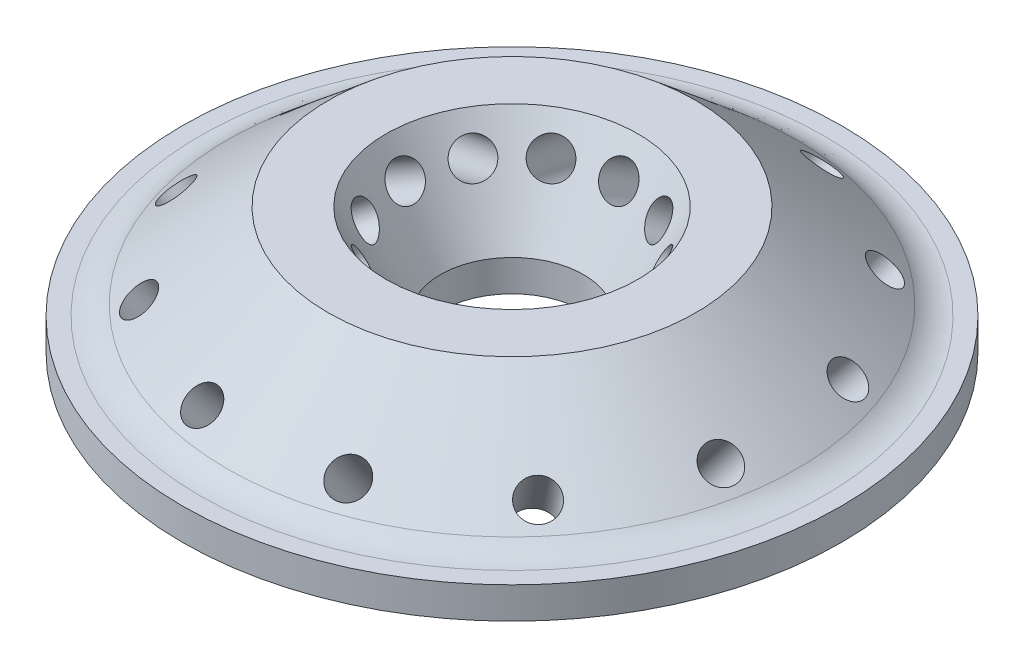
SolidWorks part; units mm, degrees
other "Markup1"
sketch "Sketch26" plane through (-39.8296, 20.32, 39.8296) normal (-0.1821, 0.7426, 0.6445) x (0.9804, 0.0872, 0.1766)
material "6061-T6 (SS)"
ref_plane "Front Plane" through (0, 0, 0) normal (0, 0, 1) x (1, 0, 0)
ref_plane "Top Plane" through (0, 0, 0) normal (0, 1, 0) x (1, 0, 0)
ref_plane "Right Plane" through (0, 0, 0) normal (1, 0, 0) x (0, 0, -1)
sketch "Sketch1" plane through (0, 0, 0) normal (0, 1, 0) x (1, 0, 0)
  circle A0 centre (0, 0) radius 69.85
  dimension "D1" = 139.7
extrude "Boss-Extrude1" add sketch "Sketch1" along normal blind 8.89
sketch "Sketch2" plane through (0, 8.89, 0) normal (0, 1, 0) x (1, 0, 0)
  circle A0 centre (0, 0) radius 15.24
  circle A1 centre (0, 0) radius 22.225
  dimension "D1" = 30.48
  dimension "D2" = 44.45
extrude "Boss-Extrude2" add sketch "Sketch2" along normal blind 11.43
sketch "Sketch7" plane through (0, 0, 0) normal (0, 0, 1) x (1, 0, 0)
  line L0 (0, 0) -> (0, 20.32) construction
  line L1 (0, 20.32) -> (-15.24, 20.32) construction
  line L2 (15.24, 20.32) -> (-15.24, 20.32) construction
  line L3 (-15.24, 20.32) -> (-15.24, 8.89)
  line L4 (-15.24, 8.89) -> (-8.6409, 8.89)
  line L5 (-15.24, 20.32) -> (-8.6409, 8.89)
  line L7 (-13.0175, 16.4705) -> (-46.2039, -2.6896) construction
  line L8 (15.24, 8.89) -> (-15.24, 8.89) construction
  point P11 (0, 0)
  dimension "D1" = 60
  dimension "D2" = 4.445
revolve "Revolve2" add sketch "Sketch7" angle 360 about L0
ref_plane "Plane2" through (0, 0, 0) normal (0.3256, 0, 0.9455) x (0, 1, 0)
sketch "Sketch9" plane through (0, 0, 0) normal (-0.3256, 0, -0.9455) x (-0.9455, 0, 0.3256)
  line L0 (0, 0) -> (0, 20.32) construction
  line L1 (0, 20.32) -> (-22.225, 20.32) construction
  line L2 (22.225, 20.32) -> (-22.225, 20.32) construction
  line L3 (-22.225, 20.32) -> (-22.225, 8.89)
  line L4 (22.225, 8.89) -> (-22.225, 8.89) construction
  line L5 (-22.225, 20.32) -> (-35.8467, 8.89)
  line L6 (-35.8467, 8.89) -> (-22.225, 8.89)
  line L7 (-31.9538, 12.1566) -> (-16.8851, -5.8015) construction
  dimension "D1" = 40
  dimension "D2" = 12.7
revolve "Revolve3" add sketch "Sketch9" angle 360 about L0
ref_plane "Plane1" through (-2.6312, -1.5191, 0) normal (-0.866, -0.5, 0) x (0.5, -0.866, 0)
sketch "Sketch13" plane through (0, 0, 0) normal (0, -1, 0) x (1, 0, 0)
  circle A0 centre (0, 0) radius 14.2875
  circle A1 centre (0, 0) radius 25.4
  circle A2 centre (0, 0) radius 33.02
  circle A3 centre (0, 0) radius 41.275
  circle A4 centre (0, 0) radius 7.62
  dimension "D1" = 28.575
  dimension "D2" = 50.8
  dimension "D3" = 66.04
  dimension "D4" = 82.55
  dimension "D5" = 15.24
extrude "Cut-Extrude10" cut sketch "Sketch13" against normal blind 5.08 contours A3 A2 | A1 A0 | A4
fillet "Fillet3" radius 2.54 5 edges at (0, 5.08, -7.62) (0, 5.08, -25.4) (0, 5.08, -14.2875) (0, 5.08, -33.02) (0, 5.08, -41.275)
sketch "Sketch10" plane through (-2.6312, -1.5191, 0) normal (-0.866, -0.5, 0) x (0.5, -0.866, 0)
  circle A0 centre (-20.7726, 0) radius 2.1828
  dimension "D1" = 4.3656
extrude "Cut-Extrude5" cut sketch "Sketch10" against normal blind 2.54 and the other way blind 30.48
ref_plane "Plane3" through (18.1431, 22.8679, -6.2472) normal (-0.6078, -0.766, 0.2093) x (0.7243, -0.6428, -0.2494)
sketch "Sketch11" plane through (18.1431, 22.8679, -6.2472) normal (-0.6078, -0.766, 0.2093) x (0.7243, -0.6428, -0.2494)
  circle A0 centre (16.6639, 0) radius 2.1828
  dimension "D1" = 4.3656
extrude "Cut-Extrude6" cut sketch "Sketch11" against normal blind 3.175 and the other way blind 19.05
pattern_circular "CirPattern1" count 12 over 360 about axis through (0, 8.89, 0) along (0, -1, 0) of "Cut-Extrude6", "Cut-Extrude5"
sketch "Sketch12" plane through (0, 8.89, 0) normal (0, 1, 0) x (1, 0, 0)
  circle A0 centre (0, 0) radius 60.96 construction
  circle A1 centre (60.96, 0) radius 2.54
  dimension "D1" = 121.92
  dimension "D2" = 5.08
extrude "Cut-Extrude7" cut sketch "Sketch12" against normal through all
pattern_circular "CirPattern2" count 12 over 360 about axis through (0, 0, 0) along (0, 1, 0) of "Cut-Extrude7"
sketch "Sketch15" plane through (0, 8.89, 0) normal (0, 1, 0) x (1, 0, 0)
  circle A0 centre (0, 0) radius 5.715 construction
  circle A1 centre (0, 5.715) radius 1.3891
  dimension "D1" = 2.7781
  dimension "D2" = 11.43
extrude "Cut-Extrude11" cut sketch "Sketch15" against normal through all
pattern_circular "CirPattern3" count 8 over 360 about axis through (0, 0, 0) along (0, 1, 0) of "Cut-Extrude11"
sketch "Sketch16" plane through (0, 0, 0) normal (0, -1, 0) x (1, 0, 0)
  circle A0 centre (0, 0) radius 27.5717
  circle A1 centre (0, 0) radius 30.2133
  dimension "D1" = 2.6416
  dimension "D2" = 60.4266
extrude "Cut-Extrude12" cut sketch "Sketch16" against normal blind 1.3208
sketch "Sketch17" plane through (0, 0, 0) normal (0, -1, 0) x (1, 0, 0)
  circle A0 centre (0, 0) radius 9.3091
  circle A1 centre (0, 0) radius 11.9507
  dimension "D1" = 2.6416
  dimension "D2" = 23.9014
extrude "Cut-Extrude13" cut sketch "Sketch17" against normal blind 1.3208
sketch "Sketch18" plane through (0, 8.89, 0) normal (0, 1, 0) x (1, 0, 0)
  circle A0 centre (0, 0) radius 49.7967
  circle A1 centre (0, 0) radius 52.4383
  dimension "D1" = 2.6416
  dimension "D2" = 104.8766
extrude "Cut-Extrude14" cut sketch "Sketch18" against normal blind 1.3208
sketch "Sketch19" plane through (0, 0, 0) normal (0, -1, 0) x (1, 0, 0)
  circle A0 centre (0, 0) radius 52.4383
  circle A1 centre (0, 0) radius 49.7967
  dimension "D1" = 104.8766
  dimension "D2" = 2.6416
extrude "Cut-Extrude15" cut sketch "Sketch19" against normal blind 1.3208
sketch "Sketch21" plane through (0, 8.89, 0) normal (0, 1, 0) x (1, 0, 0)
  circle A0 centre (0, 0) radius 1.3891
  circle A1 centre (4.0411, 4.0411) radius 1.3891 construction
extrude "Cut-Extrude17" cut sketch "Sketch21" against normal through all
fillet "Fillet2" radius 5.08 1 edges at (0, 8.89, -35.8467)
sketch "Sketch23" plane through (0, 7.5692, 0) normal (0, 1, 0) x (1, 0, 0)
  circle A0 centre (0, 0) radius 39.8296
  circle A1 centre (0, 0) radius 75.5943
extrude "Cut-Extrude18" cut sketch "Sketch23" against normal through all both and the other way through all
sketch "Sketch24" plane through (0, 0, 0) normal (0, -1, 0) x (1, 0, 0)
  circle A0 centre (0, 0) radius 58.815
extrude "Cut-Extrude19" cut sketch "Sketch24" against normal up to surface (5.08 mm away) up to face at (0, 5.08, -22.86)
sketch "Sketch25" plane through (0, 8.89, 0) normal (0, 1, 0) x (1, 0, 0)
  circle A0 centre (0, 0) radius 8.6409
  circle A1 centre (0, 0) radius 8.6409 construction
extrude "Cut-Extrude20" cut sketch "Sketch25" against normal through all
